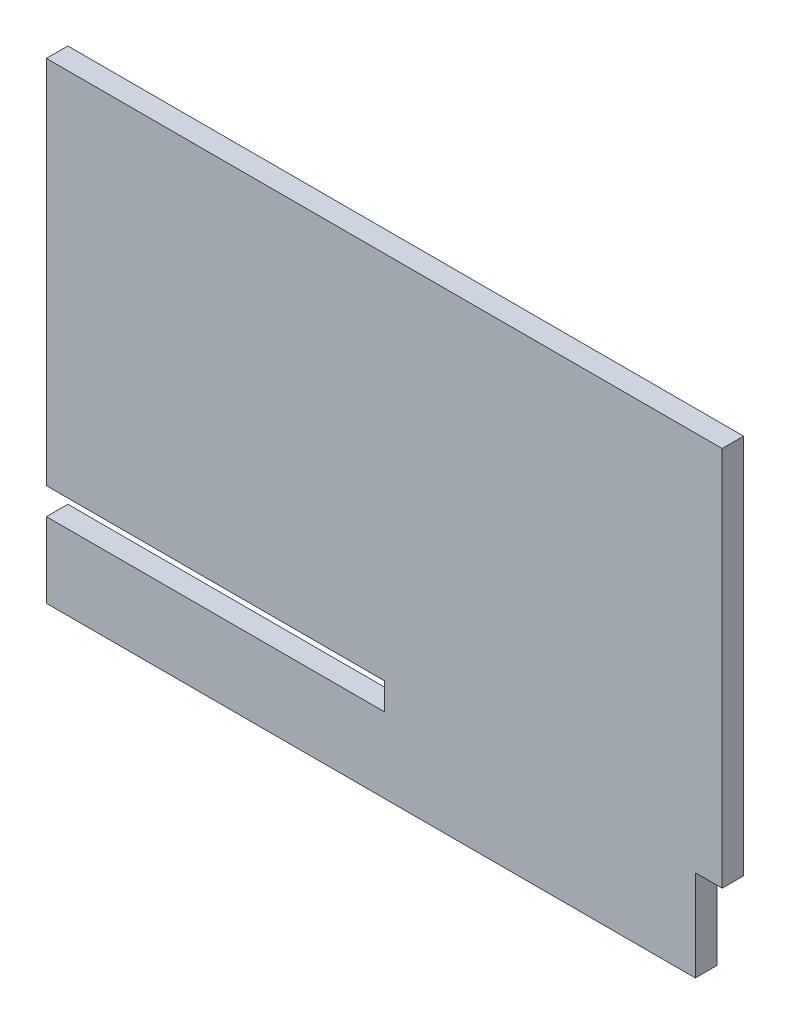
SolidWorks part; units mm, degrees
material "Acrylic (Medium-high impact)"
ref_plane "Front Plane" through (0, 0, 0) normal (0, 0, 1) x (1, 0, 0)
ref_plane "Top Plane" through (0, 0, 0) normal (0, 1, 0) x (1, 0, 0)
ref_plane "Right Plane" through (0, 0, 0) normal (1, 0, 0) x (0, 0, -1)
sketch "Sketch1" plane through (0, 0, 0) normal (0, 0, 1) x (1, 0, 0)
  line L0 (315, -135) -> (290, -135)
  line L1 (-315, 220) -> (315, 220)
  line L2 (-315, 220) -> (-315, -220)
  line L3 (-315, -220) -> (290, -220)
  line L4 (315, 220) -> (315, -135)
  line L5 (-315, 220) -> (290, -202.5397) construction
  line L6 (-315, -220) -> (315, 220) construction
  line L7 (290, -135) -> (290, -220)
  point P0 (0, 0)
  dimension "D1" = 440
  dimension "D2" = 630
  dimension "D3" = 355
  dimension "D4" = 25
extrude "Boss-Extrude1" add sketch "Sketch1" along normal blind 20
sketch "Sketch2" plane through (0, 0, 20) normal (0, 0, 1) x (1, 0, 0)
  line L0 (-315, 220) -> (-315, -220) construction
  line L1 (-630, -125) -> (0, -125)
  line L2 (-630, -125) -> (-630, -150)
  line L3 (-630, -150) -> (0, -150)
  line L4 (0, -125) -> (0, -150)
  line L5 (-630, -125) -> (0, -150) construction
  line L6 (-630, -150) -> (0, -125) construction
  line L7 (315, 220) -> (-315, 220) construction
  point P0 (-315, -137.5)
  dimension "D1" = 630
  dimension "D2" = 345
  dimension "D3" = 370
extrude "Cut-Extrude1" cut sketch "Sketch2" against normal blind 40
